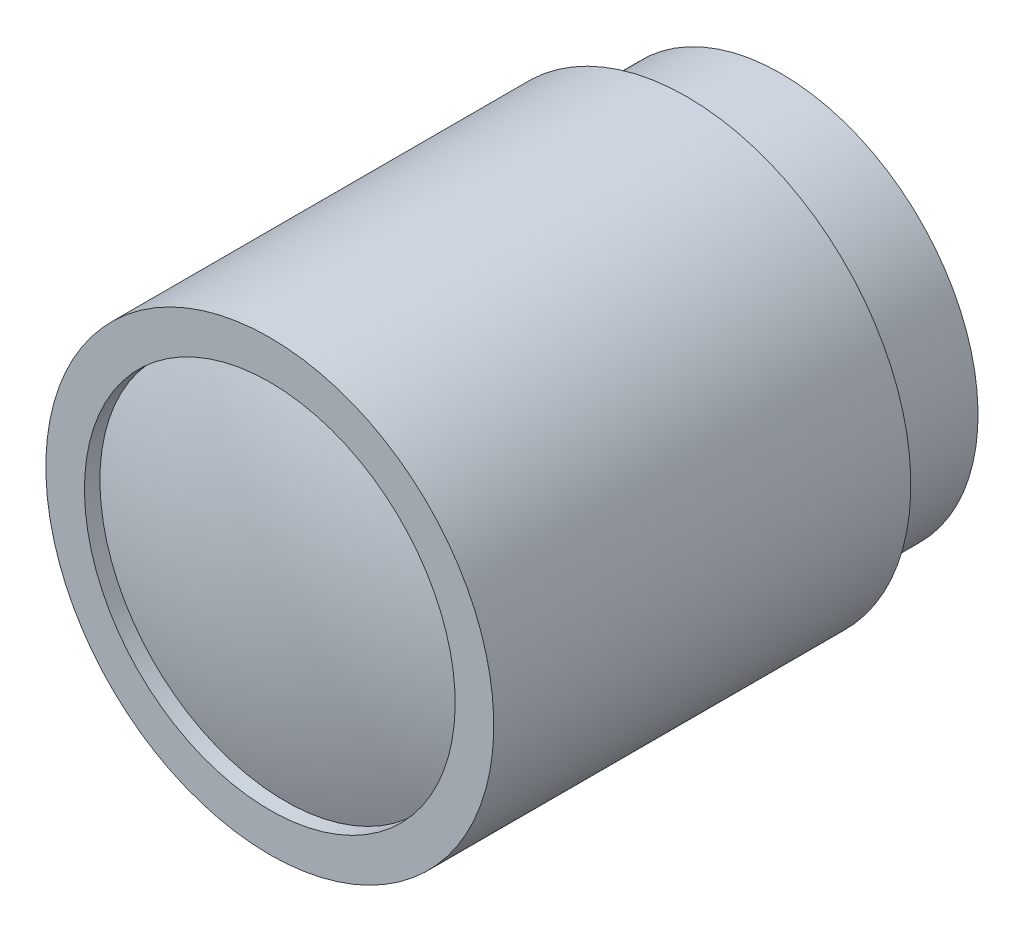
SolidWorks part; units mm, degrees
ref_plane "Front Plane" through (0, 0, 0) normal (0, 0, 1) x (1, 0, 0)
ref_plane "Top Plane" through (0, 0, 0) normal (0, 1, 0) x (1, 0, 0)
ref_plane "Right Plane" through (0, 0, 0) normal (1, 0, 0) x (0, 0, -1)
sketch "Sketch1" plane through (0, 0, 0) normal (1, 0, 0) x (0, 0, -1)
  line L0 (0, 0) -> (0, 14) construction
  line L1 (0, 14) -> (-15, 14) construction
  line L2 (-15, 14) -> (-15, 12)
  line L3 (-15, 12) -> (-14, 12)
  line L4 (18.1, 0) -> (-16, 0)
  line L5 (-22.5546, 0) -> (11.8357, 0) construction
  line L6 (-15, 14) -> (-15, 14.5)
  line L9 (-15, 14.5) -> (12, 14.5)
  line L10 (12, 14.5) -> (12, 12.75)
  line L11 (12, 12.75) -> (18.1, 12.75)
  line L12 (18.1, 12.75) -> (18.1, 0)
  arc A0 (-14, 12) -> (-16, 0) centre (21, 0) ccw
  point P9 (0, 0)
  point P16 (0, 0)
  dimension "D1" = 1
  dimension "D2" = 14
  dimension "D3" = 2
  dimension "D4" = 1
  dimension "D5" = 15
  dimension "D7" = 27
  dimension "D8" = 6.1
  dimension "D9" = 14.5
  dimension "D12" = 12.75
revolve "Revolve1" add sketch "Sketch1" angle 360 about L4
equation "\"D9@Sketch1\"=29/2"
equation "\"D12@Sketch1\"=25.5/2"
